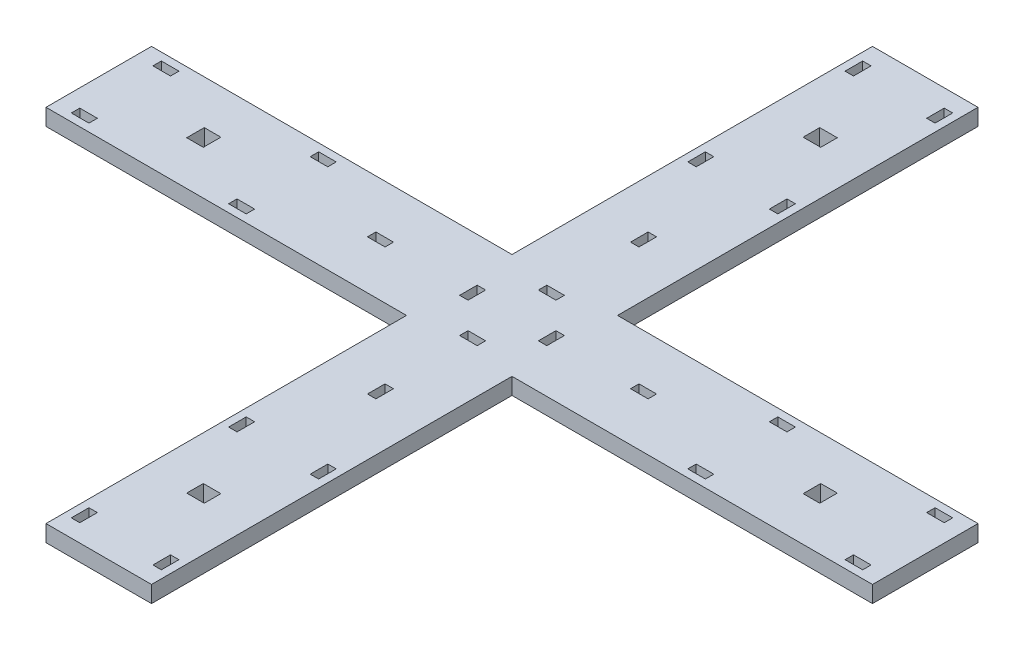
SolidWorks part; units mm, degrees
material "Acrylic (Medium-high impact)"
ref_plane "Front Plane" through (0, 0, 0) normal (0, 0, 1) x (1, 0, 0)
ref_plane "Top Plane" through (0, 0, 0) normal (0, 1, 0) x (1, 0, 0)
ref_plane "Right Plane" through (0, 0, 0) normal (1, 0, 0) x (0, 0, -1)
sketch "Sketch1" plane through (0, 0, 0) normal (0, 1, 0) x (1, 0, 0)
  line L0 (130.175, 0) -> (130.175, 130.175)
  line L1 (130.175, 130.175) -> (0, 130.175)
  line L2 (0, 130.175) -> (0, 168.275)
  line L3 (0, 168.275) -> (130.175, 168.275)
  line L4 (130.175, 168.275) -> (130.175, 298.45)
  line L5 (130.175, 298.45) -> (168.275, 298.45)
  line L6 (168.275, 298.45) -> (168.275, 168.275)
  line L7 (168.275, 168.275) -> (298.45, 168.275)
  line L8 (298.45, 168.275) -> (298.45, 130.175)
  line L9 (298.45, 130.175) -> (168.275, 130.175)
  line L10 (168.275, 130.175) -> (168.275, 0)
  line L11 (168.275, 0) -> (130.175, 0)
  line L12 (130.175, 168.275) -> (168.275, 130.175) construction
  line L13 (162.433, 12.7) -> (165.481, 12.7)
  line L14 (162.433, 12.7) -> (162.433, 6.35)
  line L15 (162.433, 6.35) -> (165.481, 6.35)
  line L16 (165.481, 12.7) -> (165.481, 6.35)
  line L17 (149.225, 0) -> (149.225, 149.225) construction
  line L18 (0, 149.225) -> (149.225, 149.225) construction
  line L19 (149.225, 298.45) -> (149.225, 149.225) construction
  line L20 (298.45, 149.225) -> (149.225, 149.225) construction
  line L21 (132.969, 12.7) -> (132.969, 6.35)
  line L22 (136.017, 6.35) -> (132.969, 6.35)
  line L23 (136.017, 12.7) -> (136.017, 6.35)
  line L24 (136.017, 12.7) -> (132.969, 12.7)
  line L25 (285.75, 162.433) -> (285.75, 165.481)
  line L26 (285.75, 162.433) -> (292.1, 162.433)
  line L27 (292.1, 162.433) -> (292.1, 165.481)
  line L28 (285.75, 165.481) -> (292.1, 165.481)
  line L29 (285.75, 132.969) -> (292.1, 132.969)
  line L30 (292.1, 136.017) -> (292.1, 132.969)
  line L31 (285.75, 136.017) -> (292.1, 136.017)
  line L32 (285.75, 136.017) -> (285.75, 132.969)
  line L33 (147.701, 193.548) -> (150.749, 193.548)
  line L34 (98.552, 150.749) -> (104.902, 150.749)
  line L35 (98.552, 150.749) -> (98.552, 147.701)
  line L36 (98.552, 147.701) -> (104.902, 147.701)
  line L37 (104.902, 150.749) -> (104.902, 147.701)
  line L38 (150.749, 199.898) -> (150.749, 193.548)
  line L39 (147.701, 199.898) -> (150.749, 199.898)
  line L40 (147.701, 199.898) -> (147.701, 193.548)
  line L41 (152.4, 164.973) -> (146.05, 164.973)
  line L42 (136.525, 146.05) -> (133.477, 146.05)
  line L43 (136.525, 146.05) -> (136.525, 152.4)
  line L44 (136.525, 152.4) -> (133.477, 152.4)
  line L45 (133.477, 146.05) -> (133.477, 152.4)
  line L46 (146.05, 161.925) -> (146.05, 164.973)
  line L47 (152.4, 161.925) -> (146.05, 161.925)
  line L48 (152.4, 161.925) -> (152.4, 164.973)
  line L49 (164.973, 146.05) -> (164.973, 152.4)
  line L50 (161.925, 152.4) -> (164.973, 152.4)
  line L51 (161.925, 146.05) -> (161.925, 152.4)
  line L52 (161.925, 146.05) -> (164.973, 146.05)
  line L53 (193.548, 150.749) -> (193.548, 147.701)
  line L54 (199.898, 147.701) -> (193.548, 147.701)
  line L55 (199.898, 150.749) -> (199.898, 147.701)
  line L56 (199.898, 150.749) -> (193.548, 150.749)
  line L57 (152.4, 136.525) -> (152.4, 133.477)
  line L58 (152.4, 136.525) -> (146.05, 136.525)
  line L59 (146.05, 136.525) -> (146.05, 133.477)
  line L60 (152.4, 133.477) -> (146.05, 133.477)
  line L61 (147.701, 98.552) -> (147.701, 104.902)
  line L62 (147.701, 98.552) -> (150.749, 98.552)
  line L63 (150.749, 98.552) -> (150.749, 104.902)
  line L64 (147.701, 104.902) -> (150.749, 104.902)
  line L65 (130.175, 37.9222) -> (168.275, 37.9222) construction
  line L66 (136.017, 63.1444) -> (132.969, 63.1444)
  line L67 (136.017, 63.1444) -> (136.017, 69.4944)
  line L68 (136.017, 69.4944) -> (132.969, 69.4944)
  line L69 (132.969, 63.1444) -> (132.969, 69.4944)
  line L70 (165.481, 63.1444) -> (165.481, 69.4944)
  line L71 (162.433, 69.4944) -> (165.481, 69.4944)
  line L72 (162.433, 63.1444) -> (162.433, 69.4944)
  line L73 (162.433, 63.1444) -> (165.481, 63.1444)
  line L74 (260.5278, 168.275) -> (260.5278, 130.175) construction
  line L75 (235.3056, 136.017) -> (235.3056, 132.969)
  line L76 (235.3056, 136.017) -> (228.9556, 136.017)
  line L77 (228.9556, 136.017) -> (228.9556, 132.969)
  line L78 (235.3056, 132.969) -> (228.9556, 132.969)
  line L79 (235.3056, 165.481) -> (228.9556, 165.481)
  line L80 (228.9556, 162.433) -> (228.9556, 165.481)
  line L81 (235.3056, 162.433) -> (228.9556, 162.433)
  line L82 (235.3056, 162.433) -> (235.3056, 165.481)
  line L83 (263.525, 152.4) -> (257.5306, 152.4)
  line L84 (152.4, 34.925) -> (146.05, 34.925)
  line L85 (152.4, 34.925) -> (152.4, 40.9194)
  line L86 (152.4, 40.9194) -> (146.05, 40.9194)
  line L87 (146.05, 34.925) -> (146.05, 40.9194)
  line L88 (257.5306, 146.05) -> (257.5306, 152.4)
  line L89 (263.525, 146.05) -> (257.5306, 146.05)
  line L90 (263.525, 146.05) -> (263.525, 152.4)
  line L91 (146.05, 263.525) -> (146.05, 257.5306)
  line L92 (152.4, 257.5306) -> (146.05, 257.5306)
  line L93 (152.4, 263.525) -> (152.4, 257.5306)
  line L94 (152.4, 263.525) -> (146.05, 263.525)
  line L95 (162.433, 235.3056) -> (165.481, 235.3056)
  line L96 (162.433, 235.3056) -> (162.433, 228.9556)
  line L97 (162.433, 228.9556) -> (165.481, 228.9556)
  line L98 (165.481, 235.3056) -> (165.481, 228.9556)
  line L99 (132.969, 235.3056) -> (132.969, 228.9556)
  line L100 (136.017, 228.9556) -> (132.969, 228.9556)
  line L101 (136.017, 235.3056) -> (136.017, 228.9556)
  line L102 (136.017, 235.3056) -> (132.969, 235.3056)
  line L103 (136.017, 285.75) -> (132.969, 285.75)
  line L104 (136.017, 285.75) -> (136.017, 292.1)
  line L105 (136.017, 292.1) -> (132.969, 292.1)
  line L106 (132.969, 285.75) -> (132.969, 292.1)
  line L107 (165.481, 285.75) -> (165.481, 292.1)
  line L108 (162.433, 292.1) -> (165.481, 292.1)
  line L109 (162.433, 285.75) -> (162.433, 292.1)
  line L110 (162.433, 285.75) -> (165.481, 285.75)
  line L111 (34.925, 146.05) -> (34.925, 152.4)
  line L112 (34.925, 146.05) -> (40.9194, 146.05)
  line L113 (40.9194, 146.05) -> (40.9194, 152.4)
  line L114 (34.925, 152.4) -> (40.9194, 152.4)
  line L115 (63.1444, 162.433) -> (63.1444, 165.481)
  line L116 (63.1444, 162.433) -> (69.4944, 162.433)
  line L117 (69.4944, 162.433) -> (69.4944, 165.481)
  line L118 (63.1444, 165.481) -> (69.4944, 165.481)
  line L119 (63.1444, 132.969) -> (69.4944, 132.969)
  line L120 (69.4944, 136.017) -> (69.4944, 132.969)
  line L121 (63.1444, 136.017) -> (69.4944, 136.017)
  line L122 (63.1444, 136.017) -> (63.1444, 132.969)
  line L123 (12.7, 136.017) -> (12.7, 132.969)
  line L124 (12.7, 136.017) -> (6.35, 136.017)
  line L125 (6.35, 136.017) -> (6.35, 132.969)
  line L126 (12.7, 132.969) -> (6.35, 132.969)
  line L127 (12.7, 165.481) -> (6.35, 165.481)
  line L128 (6.35, 162.433) -> (6.35, 165.481)
  line L129 (12.7, 162.433) -> (6.35, 162.433)
  line L130 (12.7, 162.433) -> (12.7, 165.481)
  point P38 (104.902, 149.225)
  point P43 (149.225, 193.548)
  point P48 (133.477, 149.225)
  point P53 (149.225, 164.973)
  point P62 (164.973, 149.225)
  point P63 (193.548, 149.225)
  point P72 (149.225, 133.477)
  point P73 (149.225, 104.902)
  point P98 (152.4, 37.9222)
  point P99 (149.225, 34.925)
  point P104 (263.525, 149.225)
  point P105 (260.5278, 146.05)
  point P126 (149.225, 263.525)
  point P127 (152.4, 260.5278)
  point P148 (37.9222, 146.05)
  point P149 (34.925, 149.225)
  dimension "D1" = 38.1
  dimension "D2" = 130.175
  dimension "D3" = 3.048
  dimension "D4" = 6.35
  dimension "D5" = 16.256
  dimension "D6" = 6.35
  dimension "D7" = 3.048
  dimension "D8" = 6.35
  dimension "D9" = 3.048
  dimension "D10" = 298.45
  dimension "D11" = 6.35
  dimension "D12" = 28.575
  dimension "D13" = 12.7
  dimension "D14" = 37.9222
  dimension "D15" = 5.9944
  dimension "D16" = 6.35
extrude "Boss-Extrude1" add sketch "Sketch1" along normal blind 5.9944
